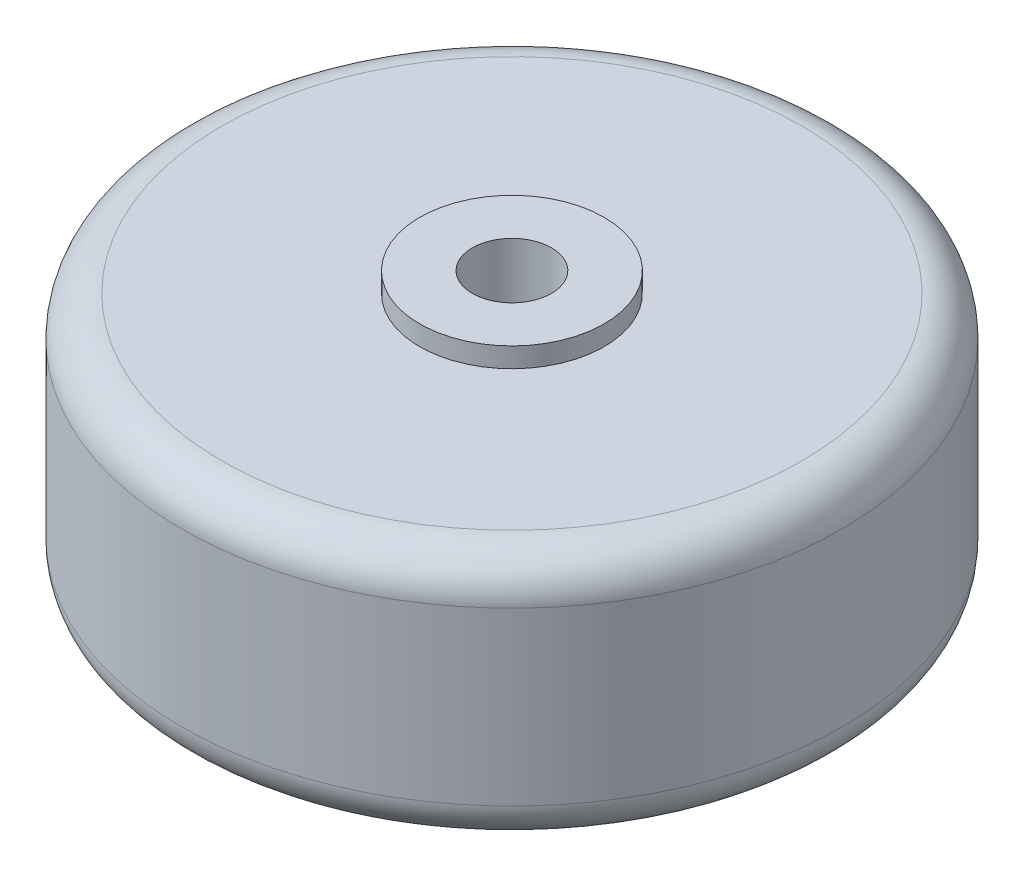
SolidWorks part; units mm, degrees
ref_plane "Front Plane" through (0, 0, 0) normal (0, 0, 1) x (1, 0, 0)
ref_plane "Top Plane" through (0, 0, 0) normal (0, 1, 0) x (1, 0, 0)
ref_plane "Right Plane" through (0, 0, 0) normal (1, 0, 0) x (0, 0, -1)
sketch "Sketch2" plane through (0, 0, 0) normal (0, 0, 1) x (1, 0, 0)
  line L0 (3, -11) -> (3, 11)
  line L1 (3, 11) -> (7, 11)
  line L2 (7, 11) -> (7, 9.5)
  line L3 (7, 9.5) -> (22, 9.5)
  line L4 (25, 6.5) -> (25, -6.5)
  line L5 (22, -9.5) -> (7, -9.5)
  line L6 (7, -9.5) -> (7, -11)
  line L7 (7, -11) -> (3, -11)
  line L8 (0, 0) -> (0, 28.1403) construction
  arc A0 (25, -6.5) -> (22, -9.5) centre (22, -6.5) cw
  arc A1 (22, 9.5) -> (25, 6.5) centre (22, 6.5) cw
  point P11 (3, 0)
  dimension "D6" = 3
  dimension "D1" = 22
  dimension "D2" = 19
  dimension "D3" = 25
  dimension "D4" = 3
  dimension "D5" = 4
revolve "Revolve2" add sketch "Sketch2" angle 360 about L8
